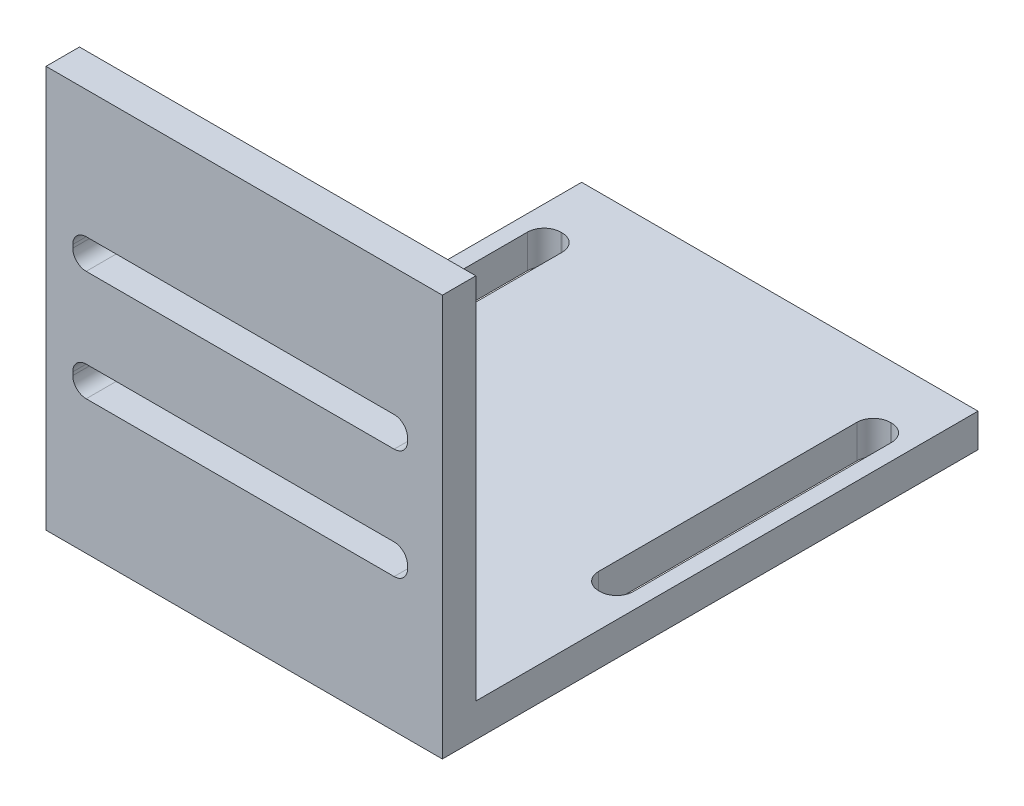
SolidWorks part; units mm, degrees
ref_plane "Front Plane" through (0, 0, 0) normal (0, 0, 1) x (1, 0, 0)
ref_plane "Top Plane" through (0, 0, 0) normal (0, 1, 0) x (1, 0, 0)
ref_plane "Right Plane" through (0, 0, 0) normal (1, 0, 0) x (0, 0, -1)
sketch "Sketch1" plane through (0, 0, 0) normal (0, 1, 0) x (1, 0, 0)
  line L1 (-18.796, 25.4) -> (18.796, 25.4)
  line L2 (-18.796, 25.4) -> (-18.796, -25.4)
  line L3 (-18.796, -25.4) -> (18.796, -25.4)
  line L4 (18.796, 25.4) -> (18.796, -25.4)
  line L5 (-18.796, 25.4) -> (18.796, -25.4) construction
  line L6 (-18.796, -25.4) -> (18.796, 25.4) construction
  point P0 (0, 0)
  dimension "D1" = 37.592
  dimension "D2" = 50.8
extrude "Boss-Extrude1" add sketch "Sketch1" along normal blind 3.175 contours L2 L3 L4 L1
sketch "Sketch2" plane through (0, 3.175, 0) normal (0, 1, 0) x (1, 0, 0)
  line L0 (18.796, 25.4) -> (18.796, -25.4) construction
  line L1 (-18.796, -25.4) -> (18.796, -25.4)
  line L2 (-18.796, -25.4) -> (-18.796, -22.225)
  line L3 (-18.796, -22.225) -> (18.796, -22.225)
  line L4 (18.796, -25.4) -> (18.796, -22.225)
  dimension "D1" = 3.175
extrude "Boss-Extrude2" add sketch "Sketch2" along normal blind 34.925
sketch "Sketch3" plane through (0, 0, 25.4) normal (0, 0, 1) x (1, 0, 0)
  line L0 (-18.796, 38.1) -> (-18.796, 0) construction
  line L1 (14.224, 12.7) -> (-14.986, 12.7)
  line L2 (15.494, 13.97) -> (15.494, 14.2748)
  line L3 (14.224, 15.5448) -> (-14.986, 15.5448)
  line L4 (-16.256, 13.97) -> (-16.256, 14.2748)
  line L5 (-18.796, 0) -> (18.796, 0) construction
  line L6 (-14.986, 23.1648) -> (14.224, 23.1648)
  line L7 (-16.256, 24.4348) -> (-16.256, 24.7396)
  line L8 (-14.986, 26.0096) -> (14.224, 26.0096)
  line L9 (15.494, 24.4348) -> (15.494, 24.7396)
  arc A0 (14.224, 23.1648) -> (15.494, 24.4348) centre (14.224, 24.4348) ccw
  arc A1 (14.224, 26.0096) -> (15.494, 24.7396) centre (14.224, 24.7396) cw
  arc A2 (-16.256, 24.7396) -> (-14.986, 26.0096) centre (-14.986, 24.7396) cw
  arc A3 (-14.986, 23.1648) -> (-16.256, 24.4348) centre (-14.986, 24.4348) cw
  arc A4 (-14.986, 15.5448) -> (-16.256, 14.2748) centre (-14.986, 14.2748) ccw
  arc A5 (-14.986, 12.7) -> (-16.256, 13.97) centre (-14.986, 13.97) cw
  arc A6 (15.494, 14.2748) -> (14.224, 15.5448) centre (14.224, 14.2748) ccw
  arc A7 (14.224, 12.7) -> (15.494, 13.97) centre (14.224, 13.97) ccw
  point P14 (15.494, 23.1648)
  point P17 (15.494, 26.0096)
  point P22 (-16.256, 23.1648)
  point P27 (-16.256, 12.7)
  point P30 (15.494, 15.5448)
  point P33 (15.494, 12.7)
  dimension "D8" = 1.27
  dimension "D1" = 2.8448
  dimension "D2" = 31.75
  dimension "D3" = 2.54
  dimension "D4" = 31.75
  dimension "D5" = 2.8448
  dimension "D6" = 7.62
  dimension "D7" = 12.7
extrude "Cut-Extrude1" cut sketch "Sketch3" against normal up to next
sketch "Sketch4" plane through (0, 0, 0) normal (0, -1, 0) x (1, 0, 0)
  line L0 (-18.796, -25.4) -> (-18.796, 25.4) construction
  line L1 (-15.5575, -20.32) -> (-15.6845, -20.32)
  line L2 (-13.97, -18.7325) -> (-13.97, 5.76)
  line L3 (-15.5575, 7.3475) -> (-15.6845, 7.3475)
  line L4 (-17.272, -18.7325) -> (-17.272, 5.76)
  line L5 (-18.796, -25.4) -> (18.796, -25.4) construction
  line L6 (18.796, -25.4) -> (18.796, 25.4) construction
  line L7 (15.6845, -20.32) -> (15.5575, -20.32)
  line L8 (17.272, -18.7325) -> (17.272, 5.76)
  line L9 (15.6845, 7.3475) -> (15.5575, 7.3475)
  line L10 (13.97, -18.7325) -> (13.97, 5.76)
  arc A0 (-13.97, 5.76) -> (-15.5575, 7.3475) centre (-15.5575, 5.76) ccw
  arc A1 (-15.6845, 7.3475) -> (-17.272, 5.76) centre (-15.6845, 5.76) ccw
  arc A2 (-15.6845, -20.32) -> (-17.272, -18.7325) centre (-15.6845, -18.7325) cw
  arc A3 (-15.5575, -20.32) -> (-13.97, -18.7325) centre (-15.5575, -18.7325) ccw
  arc A4 (17.272, 5.76) -> (15.6845, 7.3475) centre (15.6845, 5.76) ccw
  arc A5 (15.5575, 7.3475) -> (13.97, 5.76) centre (15.5575, 5.76) ccw
  arc A6 (15.5575, -20.32) -> (13.97, -18.7325) centre (15.5575, -18.7325) cw
  arc A7 (15.6845, -20.32) -> (17.272, -18.7325) centre (15.6845, -18.7325) ccw
  point P14 (-17.272, -20.32)
  point P17 (-13.97, -20.32)
  point P30 (13.97, -20.32)
  point P33 (17.272, -20.32)
  dimension "D4" = 1.5875
  dimension "D7" = 1.5875
  dimension "D1" = 3.302
  dimension "D2" = 1.524
  dimension "D3" = 5.08
  dimension "D5" = 3.302
  dimension "D6" = 1.524
extrude "Cut-Extrude2" cut sketch "Sketch4" against normal up to next
